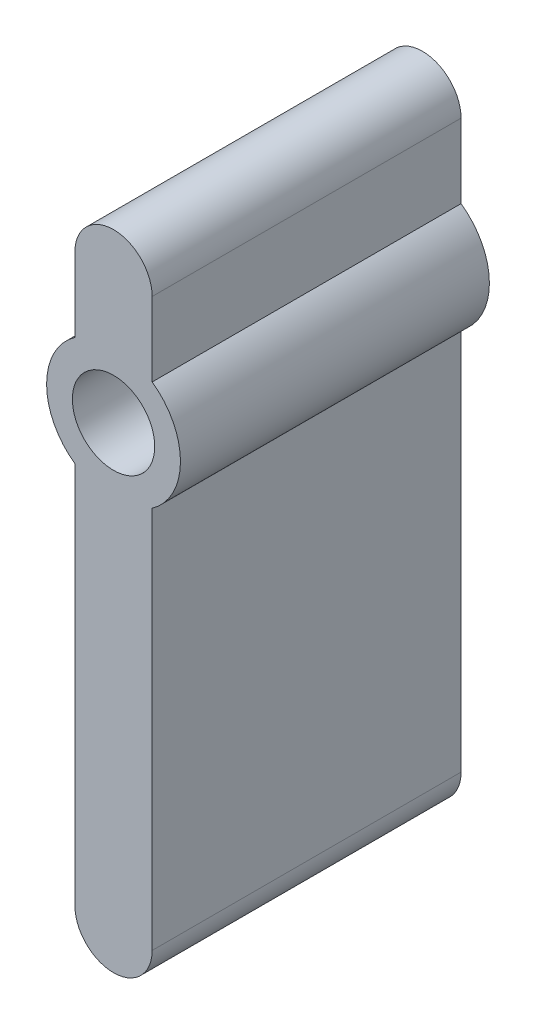
SolidWorks part; units mm, degrees
material "PLA-填充率10%"
ref_plane "前视基准面" through (0, 0, 0) normal (0, 0, 1) x (1, 0, 0)
ref_plane "上视基准面" through (0, 0, 0) normal (0, 1, 0) x (1, 0, 0)
ref_plane "右视基准面" through (0, 0, 0) normal (1, 0, 0) x (0, 0, -1)
sketch "草图1" plane through (0, 0, 0) normal (0, 0, 1) x (1, 0, 0)
  line L0 (0, 5) -> (0, -17)
  line L1 (1.5, 5) -> (1.5, -17)
  line L2 (-1.5, 5) -> (-1.5, -17)
  arc A0 (1.5, 5) -> (-1.5, 5) centre (0, 5) ccw
  arc A1 (-1.5, -17) -> (1.5, -17) centre (0, -17) ccw
  circle A2 centre (0, 0) radius 1.6
  circle A3 centre (0, 0) radius 2.6
  point P2 (0, -6)
  dimension "D1" = 3.2
  dimension "D2" = 1.5
  dimension "D5" = 1
  dimension "D3" = 5
  dimension "D4" = 22
extrude "凸台-拉伸1" add sketch "草图1" along normal blind 12
